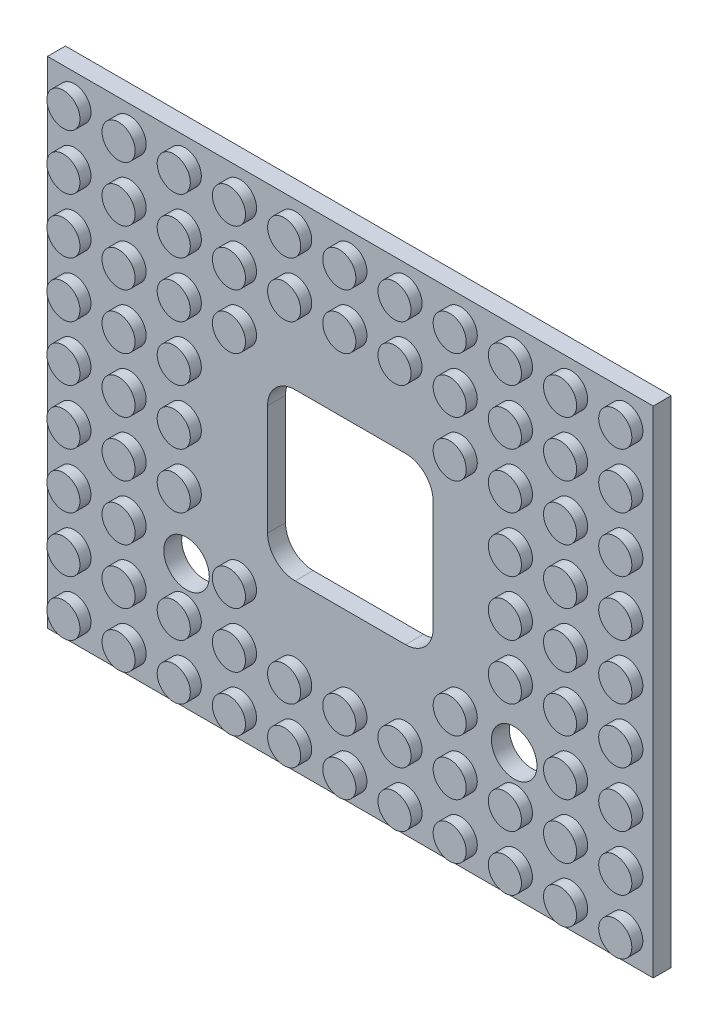
SolidWorks part; units mm, degrees
material "ABS"
ref_plane "Front Plane" through (0, 0, 0) normal (0, 0, 1) x (1, 0, 0)
ref_plane "Top Plane" through (0, 0, 0) normal (0, 1, 0) x (1, 0, 0)
ref_plane "Right Plane" through (0, 0, 0) normal (1, 0, 0) x (0, 0, -1)
sketch "Sketch1" plane through (0, 0, 0) normal (0, 0, 1) x (1, 0, 0)
  line L1 (-43.9, 35.9) -> (43.9, 35.9)
  line L2 (-43.9, 35.9) -> (-43.9, -35.9)
  line L3 (-43.9, -35.9) -> (43.9, -35.9)
  line L4 (43.9, 35.9) -> (43.9, -35.9)
  line L5 (-43.9, 35.9) -> (43.9, -35.9) construction
  line L6 (-43.9, -35.9) -> (43.9, 35.9) construction
  point P0 (0, 0)
  dimension "D1" = 87.8
  dimension "D2" = 71.8
extrude "Boss-Extrude1" add sketch "Sketch1" along normal blind 2.6
sketch "Sketch2" plane through (0, 0, 0) normal (0, 0, 1) x (1, 0, 0)
  line L1 (-8, 12) -> (8, 12)
  line L2 (-12, 8) -> (-12, -8)
  line L3 (-8, -12) -> (8, -12)
  line L4 (12, 8) -> (12, -8)
  line L5 (-12, 12) -> (12, -12) construction
  line L6 (-12, -12) -> (12, 12) construction
  arc A0 (8, -12) -> (12, -8) centre (8, -8) ccw
  arc A1 (-12, -8) -> (-8, -12) centre (-8, -8) ccw
  arc A2 (-8, 12) -> (-12, 8) centre (-8, 8) ccw
  arc A3 (8, 12) -> (12, 8) centre (8, 8) cw
  point P0 (0, 0)
  dimension "D3" = 4
  dimension "D1" = 24
  dimension "D2" = 24
extrude "Cut-Extrude1" cut sketch "Sketch2" along normal through all
sketch "Sketch4" plane through (0, 0, 2.6) normal (0, 0, 1) x (1, 0, 0)
  circle A0 centre (-23.75, -17.7) radius 3.3
  dimension "D1" = 6.6
  dimension "D2" = 17.7
  dimension "D3" = 23.75
extrude "Cut-Extrude2" cut sketch "Sketch4" against normal through all
mirror "Mirror1" about plane through (0, 0, 0) normal (1, 0, 0) of "Cut-Extrude2"
sketch "Sketch3" plane through (0, 0, 2.6) normal (0, 0, 1) x (1, 0, 0)
  circle A0 centre (-40, -32) radius 2.4
  point P5 (-52.3723, -45.8944)
  dimension "D1" = 4.8
  dimension "D2" = 32
  dimension "D3" = 40
extrude "Boss-Extrude2" add sketch "Sketch3" along normal blind 1.6
pattern_linear "LPattern1" count 9 spacing 8 along (0, 1, 0) count 11 spacing 8 along (1, 0, 0) skipping (2, 2), (2, 4), (2, 5), (2, 6), (2, 8), (3, 3), (3, 4), (3, 5), (3, 6), (3, 7), (4, 3), (4, 4), (4, 5), (4, 6), (4, 7), (5, 3), (5, 4), (5, 5), (5, 6), (5, 7), (6, 4), (6, 5), (6, 6) of "Boss-Extrude2"
